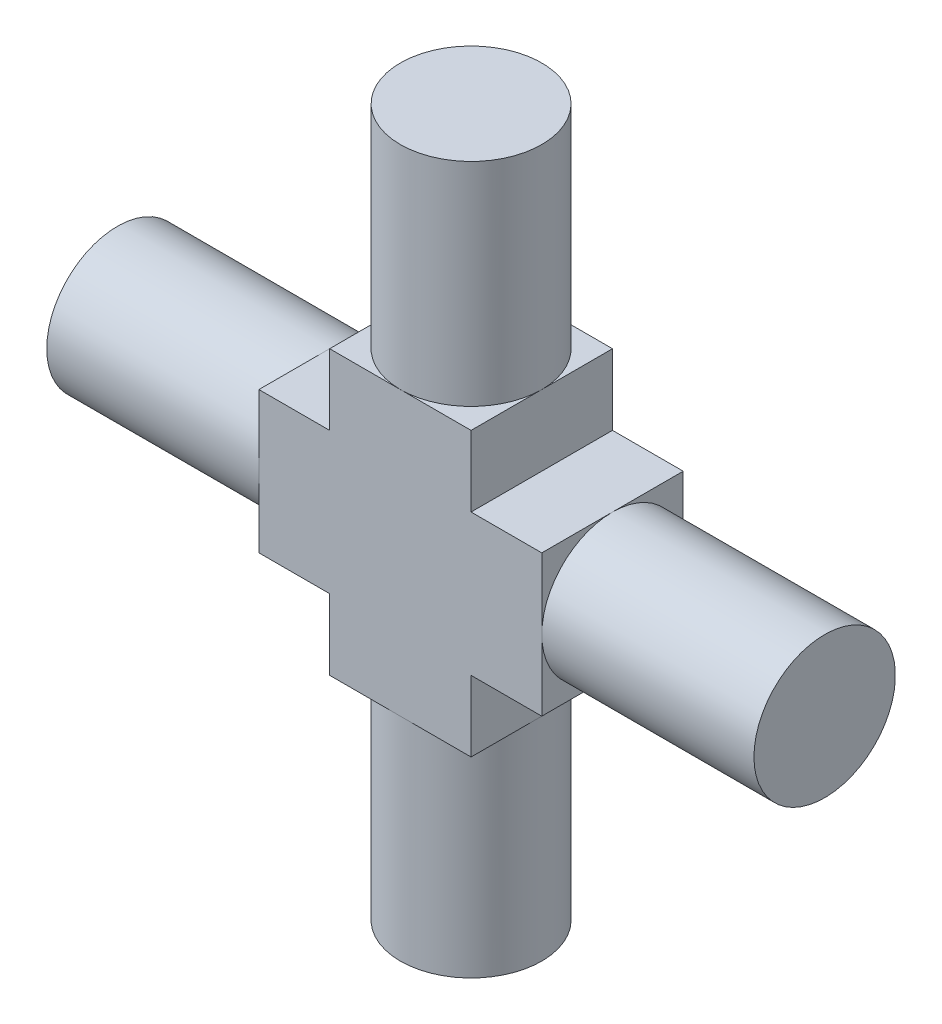
SolidWorks part; units mm, degrees
ref_plane "Front Plane" through (0, 0, 0) normal (0, 0, 1) x (1, 0, 0)
ref_plane "Top Plane" through (0, 0, 0) normal (0, 1, 0) x (1, 0, 0)
ref_plane "Right Plane" through (0, 0, 0) normal (1, 0, 0) x (0, 0, -1)
sketch "Sketch1" plane through (0, 0, 0) normal (0, 0, 1) x (1, 0, 0)
  line L0 (-2.5, 2.5) -> (-5, 2.5)
  line L1 (2.5, -2.5) -> (-2.5, -2.5) construction
  line L2 (2.5, -2.5) -> (2.5, 2.5) construction
  line L3 (2.5, 2.5) -> (-2.5, 2.5) construction
  line L4 (-2.5, -2.5) -> (-2.5, 2.5) construction
  line L5 (2.5, -2.5) -> (-2.5, 2.5) construction
  line L6 (2.5, 2.5) -> (-2.5, -2.5) construction
  line L7 (-5, 2.5) -> (-5, -2.5)
  line L8 (-5, -2.5) -> (-2.5, -2.5)
  line L9 (2.5, 2.5) -> (2.5, 5)
  line L10 (2.5, 5) -> (-2.5, 5)
  line L11 (-2.5, 5) -> (-2.5, 2.5)
  line L12 (2.5, -2.5) -> (5, -2.5)
  line L13 (5, -2.5) -> (5, 2.5)
  line L14 (5, 2.5) -> (2.5, 2.5)
  line L15 (-2.5, -2.5) -> (-2.5, -5)
  line L16 (-2.5, -5) -> (2.5, -5)
  line L17 (2.5, -5) -> (2.5, -2.5)
  point P0 (0, 0)
  point P23 (0, 0)
  dimension "D1" = 5
  dimension "D2" = 5
  dimension "D3" = 2.5
  dimension "D4" = 4
extrude "Boss-Extrude1" add sketch "Sketch1" along normal blind 5
sketch "Sketch2" plane through (0, 5, 0) normal (0, 1, 0) x (1, 0, 0)
  line L0 (0, 0) -> (0, -5) construction
  line L1 (2.5, 0) -> (-2.5, 0) construction
  line L2 (2.5, -5) -> (-2.5, -5) construction
  line L3 (-2.5, -2.5) -> (2.5, -2.5) construction
  line L4 (-2.5, -5) -> (-2.5, 0) construction
  line L5 (2.5, -5) -> (2.5, 0) construction
  circle A0 centre (0, -2.5) radius 2.5
extrude "Boss-Extrude2" add sketch "Sketch2" along normal blind 7.5
pattern_circular "CirPattern1" count 4 over 360 about axis through (0, 0, 0) along (0, 0, 1) of "Boss-Extrude2"
